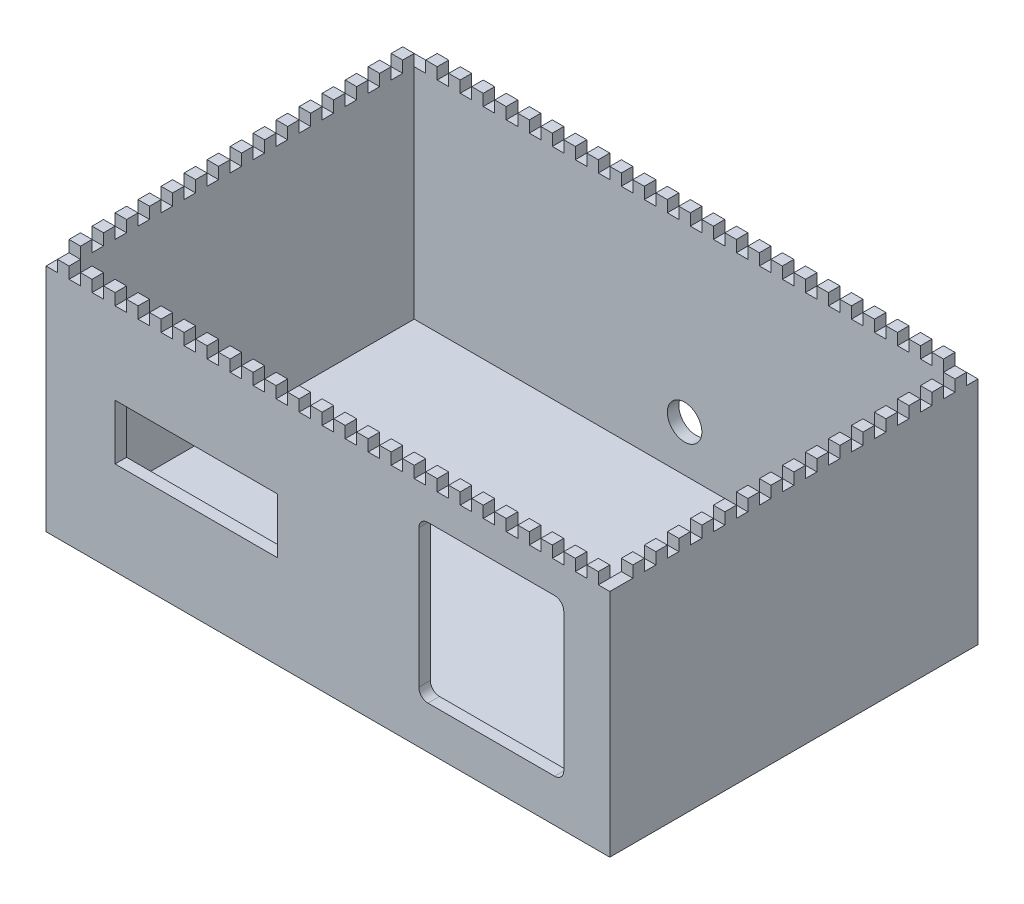
SolidWorks part; units mm, degrees
ref_plane "Alzado" through (0, 0, 0) normal (0, 0, 1) x (1, 0, 0)
ref_plane "Planta" through (0, 0, 0) normal (0, 1, 0) x (1, 0, 0)
ref_plane "Vista lateral" through (0, 0, 0) normal (1, 0, 0) x (0, 0, -1)
sketch "Croquis1" plane through (0, 0, 0) normal (0, 1, 0) x (1, 0, 0)
  line L1 (0, 0) -> (245, 0)
  line L2 (0, 0) -> (0, 160)
  line L3 (0, 160) -> (245, 160)
  line L4 (245, 0) -> (245, 160)
  dimension "D1" = 160
  dimension "D2" = 245
extrude "Saliente-Extruir1" add sketch "Croquis1" along normal blind 5
sketch "Croquis2" plane through (0, 5, 0) normal (0, 1, 0) x (1, 0, 0)
  line L0 (5, 5) -> (240, 5)
  line L1 (0, 0) -> (245, 0)
  line L2 (0, 0) -> (0, 160)
  line L3 (0, 160) -> (245, 160)
  line L4 (245, 0) -> (245, 160)
  line L5 (240, 5) -> (240, 155)
  line L6 (5, 155) -> (240, 155)
  line L7 (5, 5) -> (5, 155)
  dimension "D1" = 5
extrude "Saliente-Extruir2" add sketch "Croquis2" along normal blind 100
sketch "Croquis3" plane through (0, 0, 0) normal (0, 0, 1) x (1, 0, 0)
  line L0 (30, 52.5) -> (0, 52.5) construction
  line L1 (30, 64.5) -> (100.5, 64.5)
  line L2 (30, 64.5) -> (30, 40.5)
  line L3 (30, 40.5) -> (100.5, 40.5)
  line L4 (100.5, 64.5) -> (100.5, 40.5)
  line L5 (0, 105) -> (0, 0) construction
  line L6 (245, 52.5) -> (225, 52.5) construction
  line L7 (162, 86.5) -> (225, 86.5)
  line L8 (162, 86.5) -> (162, 18.5)
  line L9 (162, 18.5) -> (225, 18.5)
  line L10 (225, 86.5) -> (225, 18.5)
  line L11 (245, 105) -> (245, 0) construction
  dimension "D1" = 24
  dimension "D2" = 70.5
  dimension "D3" = 30
  dimension "D4" = 20
  dimension "D5" = 68
  dimension "D6" = 63
extrude "Cortar-Extruir1" cut sketch "Croquis3" against normal blind 10
fillet "Redondeo1" radius 4 4 edges at (225, 18.5, -2.5) (225, 86.5, -2.5) (162, 86.5, -2.5) (162, 18.5, -2.5)
sketch "Croquis6" plane through (0, 105, 0) normal (0, 1, 0) x (1, 0, 0)
  line L0 (0, 160) -> (0, 155)
  line L1 (0, 160) -> (0, 0) construction
  line L2 (0, 155) -> (5, 155)
  line L3 (5, 155) -> (5, 5) construction
  line L4 (5, 155) -> (5, 150)
  line L5 (5, 150) -> (0, 150)
  line L6 (0, 150) -> (0, 145)
  line L7 (0, 145) -> (5, 145)
  line L8 (5, 145) -> (5, 140)
  line L9 (5, 140) -> (0, 140)
  line L10 (0, 140) -> (0, 135)
  line L11 (0, 135) -> (5, 135)
  line L12 (5, 135) -> (5, 130)
  line L13 (5, 130) -> (0, 130)
  line L14 (0, 130) -> (0, 125)
  line L15 (0, 125) -> (5, 125)
  line L16 (5, 125) -> (5, 120)
  line L17 (5, 120) -> (0, 120)
  line L18 (0, 120) -> (0, 115)
  line L19 (0, 115) -> (5, 115)
  line L20 (5, 115) -> (5, 110)
  line L21 (5, 110) -> (0, 110)
  line L22 (0, 110) -> (0, 105)
  line L23 (0, 105) -> (5, 105)
  line L24 (5, 105) -> (5, 100)
  line L25 (5, 100) -> (0, 100)
  line L26 (0, 100) -> (0, 95)
  line L27 (0, 95) -> (5, 95)
  line L28 (5, 95) -> (5, 90)
  line L29 (5, 90) -> (0, 90)
  line L30 (0, 90) -> (0, 85)
  line L31 (0, 85) -> (5, 85)
  line L32 (5, 85) -> (5, 80)
  line L33 (5, 80) -> (0, 80)
  line L34 (0, 80) -> (0, 75)
  line L35 (0, 75) -> (5, 75)
  line L36 (5, 75) -> (5, 70)
  line L37 (5, 70) -> (0, 70)
  line L38 (0, 70) -> (0, 65)
  line L39 (0, 65) -> (5, 65)
  line L40 (5, 65) -> (5, 60)
  line L41 (5, 60) -> (0, 60)
  line L42 (0, 60) -> (0, 55)
  line L43 (0, 55) -> (5, 55)
  line L44 (5, 55) -> (5, 50)
  line L45 (5, 50) -> (0, 50)
  line L46 (0, 50) -> (0, 45)
  line L47 (0, 45) -> (5, 45)
  line L48 (5, 45) -> (5, 40)
  line L49 (5, 40) -> (0, 40)
  line L50 (0, 40) -> (0, 35)
  line L51 (0, 35) -> (5, 35)
  line L52 (5, 35) -> (5, 30)
  line L53 (5, 30) -> (0, 30)
  line L54 (0, 30) -> (0, 25)
  line L55 (0, 25) -> (5, 25)
  line L56 (5, 25) -> (5, 20)
  line L57 (5, 20) -> (0, 20)
  line L58 (0, 20) -> (0, 15)
  line L59 (0, 15) -> (5, 15)
  line L60 (5, 15) -> (5, 10)
  line L61 (5, 10) -> (0, 10)
  line L62 (122.5, 155) -> (122.5, 140) construction
  line L63 (240, 155) -> (5, 155) construction
  line L64 (240, 10) -> (245, 10)
  line L65 (240, 15) -> (240, 10)
  line L66 (245, 15) -> (240, 15)
  line L67 (245, 20) -> (245, 15)
  line L68 (240, 20) -> (245, 20)
  line L69 (240, 25) -> (240, 20)
  line L70 (245, 25) -> (240, 25)
  line L71 (245, 30) -> (245, 25)
  line L72 (240, 30) -> (245, 30)
  line L73 (240, 35) -> (240, 30)
  line L74 (245, 35) -> (240, 35)
  line L75 (245, 40) -> (245, 35)
  line L76 (240, 40) -> (245, 40)
  line L77 (240, 45) -> (240, 40)
  line L78 (245, 45) -> (240, 45)
  line L79 (245, 50) -> (245, 45)
  line L80 (240, 50) -> (245, 50)
  line L81 (240, 55) -> (240, 50)
  line L82 (245, 55) -> (240, 55)
  line L83 (245, 60) -> (245, 55)
  line L84 (240, 60) -> (245, 60)
  line L85 (240, 65) -> (240, 60)
  line L86 (245, 65) -> (240, 65)
  line L87 (245, 70) -> (245, 65)
  line L88 (240, 70) -> (245, 70)
  line L89 (240, 75) -> (240, 70)
  line L90 (245, 75) -> (240, 75)
  line L91 (245, 80) -> (245, 75)
  line L92 (240, 80) -> (245, 80)
  line L93 (240, 85) -> (240, 80)
  line L94 (245, 85) -> (240, 85)
  line L95 (245, 90) -> (245, 85)
  line L96 (240, 90) -> (245, 90)
  line L97 (240, 95) -> (240, 90)
  line L98 (245, 95) -> (240, 95)
  line L99 (245, 100) -> (245, 95)
  line L100 (240, 100) -> (245, 100)
  line L101 (240, 105) -> (240, 100)
  line L102 (245, 105) -> (240, 105)
  line L103 (245, 110) -> (245, 105)
  line L104 (240, 110) -> (245, 110)
  line L105 (240, 115) -> (240, 110)
  line L106 (245, 115) -> (240, 115)
  line L107 (245, 120) -> (245, 115)
  line L108 (240, 120) -> (245, 120)
  line L109 (240, 125) -> (240, 120)
  line L110 (245, 125) -> (240, 125)
  line L111 (245, 130) -> (245, 125)
  line L112 (240, 130) -> (245, 130)
  line L113 (240, 135) -> (240, 130)
  line L114 (245, 135) -> (240, 135)
  line L115 (245, 140) -> (245, 135)
  line L116 (240, 140) -> (245, 140)
  line L117 (240, 145) -> (240, 140)
  line L118 (245, 145) -> (240, 145)
  line L119 (245, 150) -> (245, 145)
  line L120 (240, 150) -> (245, 150)
  line L121 (240, 155) -> (240, 150)
  line L122 (245, 155) -> (240, 155)
  line L123 (245, 160) -> (245, 155)
  line L124 (0, 160) -> (10, 160)
  line L125 (245, 160) -> (0, 160) construction
  line L126 (10, 160) -> (10, 155)
  line L127 (10, 155) -> (15, 155)
  line L128 (15, 155) -> (15, 160)
  line L129 (15, 160) -> (20, 160)
  line L130 (20, 160) -> (20, 155)
  line L131 (20, 155) -> (25, 155)
  line L132 (25, 155) -> (25, 160)
  line L133 (25, 160) -> (30, 160)
  line L134 (30, 160) -> (30, 155)
  line L135 (30, 155) -> (35, 155)
  line L136 (35, 155) -> (35, 160)
  line L137 (35, 160) -> (40, 160)
  line L138 (40, 160) -> (40, 155)
  line L139 (40, 155) -> (45, 155)
  line L140 (45, 155) -> (45, 160)
  line L141 (45, 160) -> (50, 160)
  line L142 (50, 160) -> (50, 155)
  line L143 (50, 155) -> (55, 155)
  line L144 (55, 155) -> (55, 160)
  line L145 (55, 160) -> (60, 160)
  line L146 (60, 160) -> (60, 155)
  line L147 (60, 155) -> (65, 155)
  line L148 (65, 155) -> (65, 160)
  line L149 (65, 160) -> (70, 160)
  line L150 (70, 160) -> (70, 155)
  line L151 (70, 155) -> (75, 155)
  line L152 (75, 155) -> (75, 160)
  line L153 (75, 160) -> (80, 160)
  line L154 (80, 160) -> (80, 155)
  line L155 (80, 155) -> (85, 155)
  line L156 (85, 155) -> (85, 160)
  line L157 (85, 160) -> (90, 160)
  line L158 (90, 160) -> (90, 155)
  line L159 (90, 155) -> (95, 155)
  line L160 (95, 155) -> (95, 160)
  line L161 (95, 160) -> (100, 160)
  line L162 (100, 160) -> (100, 155)
  line L163 (100, 155) -> (105, 155)
  line L164 (105, 155) -> (105, 160)
  line L165 (105, 160) -> (110, 160)
  line L166 (110, 160) -> (110, 155)
  line L167 (110, 155) -> (115, 155)
  line L168 (115, 155) -> (115, 160)
  line L169 (115, 160) -> (120, 160)
  line L170 (120, 160) -> (120, 155)
  line L171 (120, 155) -> (125, 155)
  line L172 (125, 155) -> (125, 160)
  line L173 (125, 160) -> (130, 160)
  line L174 (130, 160) -> (130, 155)
  line L175 (130, 155) -> (135, 155)
  line L176 (135, 155) -> (135, 160)
  line L177 (135, 160) -> (140, 160)
  line L178 (140, 160) -> (140, 155)
  line L179 (140, 155) -> (145, 155)
  line L180 (145, 155) -> (145, 160)
  line L181 (145, 160) -> (150, 160)
  line L182 (150, 160) -> (150, 155)
  line L183 (150, 155) -> (155, 155)
  line L184 (155, 155) -> (155, 160)
  line L185 (155, 160) -> (160, 160)
  line L186 (160, 160) -> (160, 155)
  line L187 (160, 155) -> (165, 155)
  line L188 (165, 155) -> (165, 160)
  line L189 (165, 160) -> (170, 160)
  line L190 (170, 160) -> (170, 155)
  line L191 (170, 155) -> (175, 155)
  line L192 (175, 155) -> (175, 160)
  line L193 (175, 160) -> (180, 160)
  line L194 (180, 160) -> (180, 155)
  line L195 (180, 155) -> (185, 155)
  line L196 (185, 155) -> (185, 160)
  line L197 (185, 160) -> (190, 160)
  line L198 (190, 160) -> (190, 155)
  line L199 (190, 155) -> (195, 155)
  line L200 (195, 155) -> (195, 160)
  line L201 (195, 160) -> (200, 160)
  line L202 (200, 160) -> (200, 155)
  line L203 (200, 155) -> (205, 155)
  line L204 (205, 155) -> (205, 160)
  line L205 (205, 160) -> (210, 160)
  line L206 (210, 160) -> (210, 155)
  line L207 (210, 155) -> (215, 155)
  line L208 (215, 155) -> (215, 160)
  line L209 (215, 160) -> (220, 160)
  line L210 (220, 160) -> (220, 155)
  line L211 (220, 155) -> (225, 155)
  line L212 (225, 155) -> (225, 160)
  line L213 (225, 160) -> (230, 160)
  line L214 (230, 160) -> (230, 155)
  line L215 (230, 155) -> (235, 155)
  line L216 (235, 155) -> (235, 160)
  line L217 (235, 160) -> (240, 160)
  line L218 (240, 160) -> (245, 160)
  line L219 (0, 10) -> (0, 0)
  line L220 (0, 0) -> (5, 0)
  line L221 (0, 0) -> (245, 0) construction
  line L222 (5, 0) -> (5, 5)
  line L223 (5, 5) -> (10, 5)
  line L224 (5, 5) -> (240, 5) construction
  line L225 (10, 5) -> (10, 0)
  line L226 (10, 0) -> (15, 0)
  line L227 (15, 0) -> (15, 5)
  line L228 (15, 5) -> (20, 5)
  line L229 (20, 5) -> (20, 0)
  line L230 (20, 0) -> (25, 0)
  line L231 (25, 0) -> (25, 5)
  line L232 (25, 5) -> (30, 5)
  line L233 (30, 5) -> (30, 0)
  line L234 (30, 0) -> (35, 0)
  line L235 (35, 0) -> (35, 5)
  line L236 (35, 5) -> (40, 5)
  line L237 (40, 5) -> (40, 0)
  line L238 (40, 0) -> (45, 0)
  line L239 (45, 0) -> (45, 5)
  line L240 (45, 5) -> (50, 5)
  line L241 (50, 5) -> (50, 0)
  line L242 (50, 0) -> (55, 0)
  line L243 (55, 0) -> (55, 5)
  line L244 (55, 5) -> (60, 5)
  line L245 (60, 5) -> (60, 0)
  line L246 (60, 0) -> (65, 0)
  line L247 (65, 0) -> (65, 5)
  line L248 (65, 5) -> (70, 5)
  line L249 (70, 5) -> (70, 0)
  line L250 (70, 0) -> (75, 0)
  line L251 (75, 0) -> (75, 5)
  line L252 (75, 5) -> (80, 5)
  line L253 (80, 5) -> (80, 0)
  line L254 (80, 0) -> (85, 0)
  line L255 (85, 0) -> (85, 5)
  line L256 (85, 5) -> (90, 5)
  line L257 (90, 5) -> (90, 0)
  line L258 (90, 0) -> (95, 0)
  line L259 (95, 0) -> (95, 5)
  line L260 (95, 5) -> (100, 5)
  line L261 (100, 5) -> (100, 0)
  line L262 (100, 0) -> (105, 0)
  line L263 (105, 0) -> (105, 5)
  line L264 (105, 5) -> (110, 5)
  line L265 (110, 5) -> (110, 0)
  line L266 (110, 0) -> (115, 0)
  line L267 (115, 0) -> (115, 5)
  line L268 (115, 5) -> (120, 5)
  line L269 (120, 5) -> (120, 0)
  line L270 (120, 0) -> (125, 0)
  line L271 (125, 0) -> (125, 5)
  line L272 (125, 5) -> (130, 5)
  line L273 (130, 5) -> (130, 0)
  line L274 (130, 0) -> (135, 0)
  line L275 (135, 0) -> (135, 5)
  line L276 (135, 5) -> (140, 5)
  line L277 (140, 5) -> (140, 0)
  line L278 (140, 0) -> (145, 0)
  line L279 (145, 0) -> (145, 5)
  line L280 (145, 5) -> (150, 5)
  line L281 (150, 5) -> (150, 0)
  line L282 (150, 0) -> (155, 0)
  line L283 (155, 0) -> (155, 5)
  line L284 (155, 5) -> (160, 5)
  line L285 (160, 5) -> (160, 0)
  line L286 (160, 0) -> (165, 0)
  line L287 (165, 0) -> (165, 5)
  line L288 (165, 5) -> (170, 5)
  line L289 (170, 5) -> (170, 0)
  line L290 (170, 0) -> (175, 0)
  line L291 (175, 0) -> (175, 5)
  line L292 (175, 5) -> (180, 5)
  line L293 (180, 5) -> (180, 0)
  line L294 (180, 0) -> (185, 0)
  line L295 (185, 0) -> (185, 5)
  line L296 (185, 5) -> (190, 5)
  line L297 (190, 5) -> (190, 0)
  line L298 (190, 0) -> (195, 0)
  line L299 (195, 0) -> (195, 5)
  line L300 (195, 5) -> (200, 5)
  line L301 (200, 5) -> (200, 0)
  line L302 (200, 0) -> (205, 0)
  line L303 (205, 0) -> (205, 5)
  line L304 (205, 5) -> (210, 5)
  line L305 (210, 5) -> (210, 0)
  line L306 (210, 0) -> (215, 0)
  line L307 (215, 0) -> (215, 5)
  line L308 (215, 5) -> (220, 5)
  line L309 (220, 5) -> (220, 0)
  line L310 (220, 0) -> (225, 0)
  line L311 (225, 0) -> (225, 5)
  line L312 (225, 5) -> (230, 5)
  line L313 (230, 5) -> (230, 0)
  line L314 (230, 0) -> (235, 0)
  line L315 (235, 0) -> (235, 5)
  line L316 (235, 5) -> (240, 5)
  line L317 (240, 5) -> (240, 0)
  line L318 (240, 0) -> (245, 0)
  line L319 (245, 0) -> (245, 10)
  dimension "D1" = 5
  dimension "D2" = 15
  dimension "D3" = 5
  dimension "D4" = 10
  dimension "D6" = 24
  dimension "D7" = 5
  dimension "D5" = 23
extrude "Cortar-Extruir2" cut sketch "Croquis6" against normal blind 5
sketch "Croquis8" plane through (0, 0, -160) normal (0, 0, -1) x (-1, 0, 0)
  line L0 (-245, 0) -> (0, 0) construction
  line L1 (-122.5, 0) -> (-122.5, 25) construction
  circle A0 centre (-122.5, 25) radius 7.5
  dimension "D1" = 25
  dimension "D2" = 15
extrude "Cortar-Extruir3" cut sketch "Croquis8" against normal blind 10
